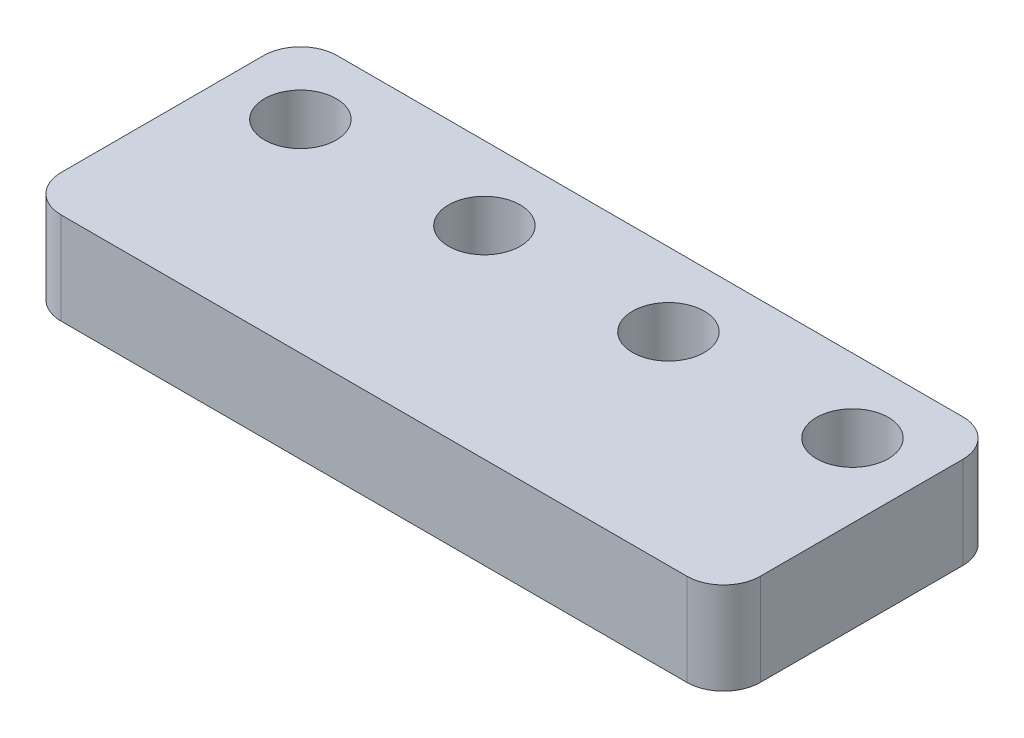
SolidWorks part; units mm, degrees
ref_plane "Front Plane" through (0, 0, 0) normal (0, 0, 1) x (1, 0, 0)
ref_plane "Top Plane" through (0, 0, 0) normal (0, 1, 0) x (1, 0, 0)
ref_plane "Right Plane" through (0, 0, 0) normal (1, 0, 0) x (0, 0, -1)
sketch "Sketch1" plane through (0, 0, 0) normal (0, 1, 0) x (1, 0, 0)
  line L1 (-36, 0) -> (-2, 0)
  line L2 (-38, -2) -> (-38, -13)
  line L3 (-36, -15) -> (-2, -15)
  line L4 (0, -2) -> (0, -13)
  arc A0 (-2, -15) -> (0, -13) centre (-2, -13) ccw
  arc A1 (-38, -13) -> (-36, -15) centre (-36, -13) ccw
  arc A2 (-36, 0) -> (-38, -2) centre (-36, -2) ccw
  arc A3 (-2, 0) -> (0, -2) centre (-2, -2) cw
  point P7 (0, -15)
  point P12 (-38, 0)
  point P15 (0, 0)
  dimension "D3" = 2
  dimension "D1" = 38
  dimension "D2" = 15
extrude "Boss-Extrude1" add sketch "Sketch1" along normal blind 5
sketch "Sketch2" plane through (0, 5, 0) normal (0, 1, 0) x (1, 0, 0)
  line L2 (-4, -4) -> (-54, -4) construction
  line L10 (-2, 0) -> (-36, 0) construction
  line L11 (0, -13) -> (0, -2) construction
  circle A20 centre (-4, -4) radius 1.95
  circle A21 centre (-14, -4) radius 1.95
  circle A22 centre (-24, -4) radius 1.95
  circle A23 centre (-54, -4) radius 1.95
  circle A24 centre (-34, -4) radius 1.95
  circle A25 centre (-44, -4) radius 1.95
  dimension "D1" = 4
  dimension "D4" = 10
  dimension "D7" = 3.9
  dimension "D8" = 3.9
  dimension "D9" = 3.9
  dimension "D10" = 3.9
  dimension "D11" = 10
  dimension "D12" = 10
  dimension "D13" = 10
  dimension "D5" = 3.9
  dimension "D6" = 3.9
  dimension "D2" = 4
  dimension "D3" = 10
extrude "Cut-Extrude1" cut sketch "Sketch2" against normal through all
